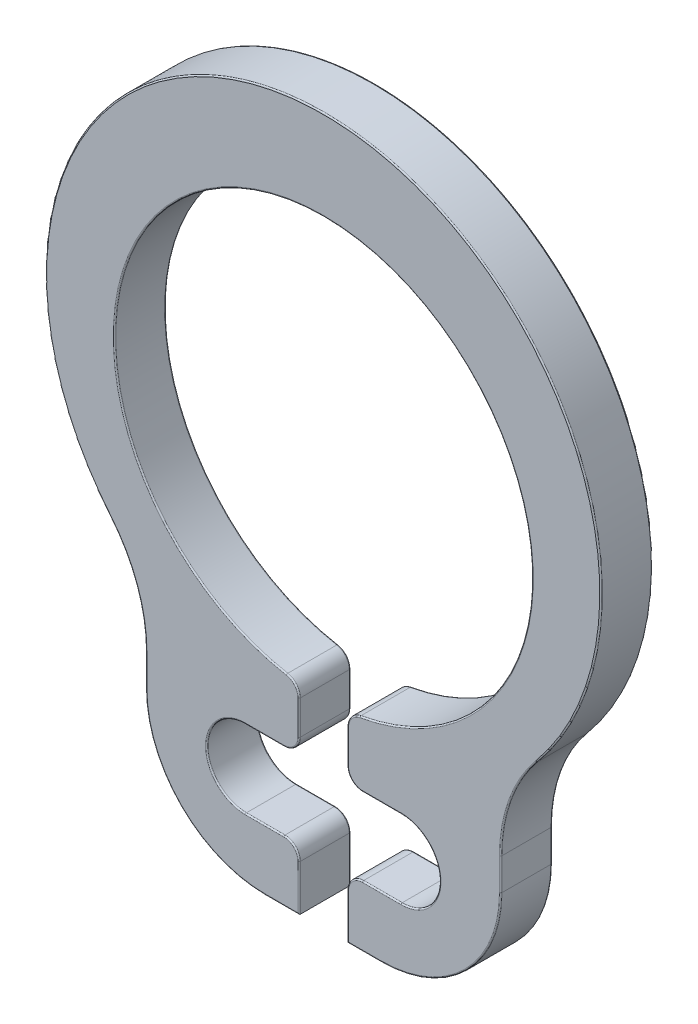
SolidWorks part; units mm, degrees
material "PLA"
ref_plane "Front Plane" through (0, 0, 0) normal (0, 0, 1) x (1, 0, 0)
ref_plane "Top Plane" through (0, 0, 0) normal (0, 1, 0) x (1, 0, 0)
ref_plane "Right Plane" through (0, 0, 0) normal (1, 0, 0) x (0, 0, -1)
sketch "Sketch1" plane through (0, 0, 0) normal (0, 0, 1) x (1, 0, 0)
  line L0 (0, 5.5) -> (0, -5.5) construction
  line L1 (-1.2125, -3.95) -> (1.2125, -3.95) construction
  line L2 (-1.2125, -3.35) -> (1.2125, -3.35)
  line L3 (-1.2125, -4.55) -> (1.2125, -4.55)
  line L4 (1.8125, -3.95) -> (2.7625, -3.95) construction
  line L5 (0, -2.4) -> (0, -3.35) construction
  circle A0 centre (0, 0.85) radius 3.25
  arc A3 (-1.2125, -3.35) -> (-1.2125, -4.55) centre (-1.2125, -3.95) ccw
  arc A4 (1.2125, -4.55) -> (1.2125, -3.35) centre (1.2125, -3.95) ccw
  circle A5 centre (0, 1.175) radius 4.325 construction
  circle A6 centre (0, 0.85) radius 3.5 construction
  circle A7 centre (0, 0.85) radius 3.35 construction
  point P6 (0, 4.1)
  point P7 (0, -2.4)
  point P10 (0, -3.95)
  dimension "For OD" = 7
  dimension "ID" = 6.5
  dimension "Band Width" = 1.4
  dimension "Tap Height" = 3.1
  dimension "Tap ID" = 1.2
  dimension "D3" = 1.55
  dimension "Tap Width Ref" = 5.525
  dimension "D1" = 0.325
sketch "Sketch2" plane through (0, 0, 0) normal (1, 0, 0) x (0, 0, -1)
  line L0 (-0.4, 5.5) -> (0.4, 5.5) construction
  line L1 (0, 7.2) -> (0, -5.5) construction
  line L2 (0, 5.5) -> (0, -5.5) construction
  line L3 (-0.45, 7.2) -> (0.45, 7.2) construction
  line L4 (-0.45, -5.5) -> (0.45, -5.5) construction
  dimension "Thickness" = 0.8
  dimension "For Groove Width" = 0.9
sketch "Sketch3" plane through (0, 0, 0) normal (0, 0, 1) x (1, 0, 0)
  line L0 (-1.2125, -4.55) -> (1.2125, -4.55) construction
  line L1 (-1.2125, -3.35) -> (1.2125, -3.35) construction
  line L2 (-1.2125, -4.55) -> (1.2125, -4.55)
  line L3 (-1.2125, -3.35) -> (1.2125, -3.35)
  line L4 (2.7625, -3.1428) -> (2.7625, -3.64)
  line L5 (-0.9025, -5.5) -> (0.9025, -5.5)
  line L6 (-2.7625, -3.1428) -> (-2.7625, -3.64)
  line L7 (-1.8125, -3.95) -> (-2.7625, -3.95) construction
  line L8 (1.8125, -3.95) -> (2.7625, -3.95) construction
  arc A0 (-1.2125, -3.35) -> (-1.2125, -4.55) centre (-1.2125, -3.95) ccw construction
  arc A1 (1.2125, -4.55) -> (1.2125, -3.35) centre (1.2125, -3.95) ccw construction
  arc A2 (-1.2125, -3.35) -> (-1.2125, -4.55) centre (-1.2125, -3.95) ccw
  arc A3 (1.2125, -4.55) -> (1.2125, -3.35) centre (1.2125, -3.95) ccw
  circle A4 centre (0, 0.85) radius 3.25 construction
  circle A5 centre (0, 0.85) radius 3.25
  arc A6 (-3.3234, -1.5928) -> (3.3234, -1.5928) centre (0, 1.175) cw
  arc A8 (3.3234, -1.5928) -> (2.7625, -3.1428) centre (5.1846, -3.1428) ccw
  arc A9 (2.7625, -3.64) -> (0.9025, -5.5) centre (0.9025, -3.64) cw
  arc A10 (-3.3234, -1.5928) -> (-2.7625, -3.1428) centre (-5.1846, -3.1428) cw
  arc A11 (-2.7625, -3.64) -> (-0.9025, -5.5) centre (-0.9025, -3.64) ccw
  circle A12 centre (0, 1.175) radius 4.325 construction
  dimension "D1" = 1.55
  dimension "D2" = 1.86
  dimension "D3" = 0.95
extrude "Boss-Extrude1" add sketch "Sketch3" along normal mid plane 0.8
sketch "Sketch4" plane through (0, 0, 0) normal (0, 0, 1) x (1, 0, 0)
  line L0 (0, 0.85) -> (0, -5.5)
extrude "Cut-Extrude-Thin1" cut sketch "Sketch4" against normal through all both and the other way through all thin thin type mid plane wall 0.75
fillet "Fillet2" radius 0.2375 6 edges at (0.375, -4.55, 0) (-0.375, -4.55, 0) (0.375, -3.35, 0) (0.375, -2.3783, 0) (-0.375, -3.35, 0) (-0.375, -2.3783, 0)
fillet "Fillet1" radius 0.02 52 edges at (-0.9125, -4.55, -0.4) (-1.8125, -3.95, -0.4) (-0.9125, -3.35, -0.4) (0, 4.1, -0.4) (0.9125, -3.35, -0.4) (1.8125, -3.95, -0.4) (0.9125, -4.55, -0.4) (0.375, -5.1438, -0.4) (0.6388, -5.5, -0.4) (2.2177, -4.9552, -0.4) (2.7625, -3.3914, -0.4) (2.907, -2.3186, -0.4) (0, 5.5, -0.4) (-2.907, -2.3186, -0.4) (-2.7625, -3.3914, -0.4) (-2.2177, -4.9552, -0.4) (-0.6388, -5.5, -0.4) (-0.375, -5.1438, -0.4) (-2.2177, -4.9552, 0.4) (-2.7625, -3.3914, 0.4) (-2.907, -2.3186, 0.4) (0, 5.5, 0.4) (2.907, -2.3186, 0.4) (2.7625, -3.3914, 0.4) (2.2177, -4.9552, 0.4) (0.6388, -5.5, 0.4) (0.375, -5.1438, 0.4) (0.9125, -4.55, 0.4) (1.8125, -3.95, 0.4) (0.9125, -3.35, 0.4) (0, 4.1, 0.4) (-0.9125, -3.35, 0.4) (-1.8125, -3.95, 0.4) (-0.9125, -4.55, 0.4) (-0.375, -5.1438, 0.4) (-0.6388, -5.5, 0.4) (-0.4446, -4.6196, -0.4) (-0.4446, -3.2804, -0.4) (-0.375, -2.8479, -0.4) (-0.4304, -2.4308, -0.4) (0.4304, -2.4308, -0.4) (0.375, -2.8479, -0.4) (0.4446, -3.2804, -0.4) (0.4446, -4.6196, -0.4) (0.4446, -3.2804, 0.4) (0.375, -2.8479, 0.4) (0.4304, -2.4308, 0.4) (-0.4304, -2.4308, 0.4) (-0.375, -2.8479, 0.4) (-0.4446, -3.2804, 0.4) (-0.4446, -4.6196, 0.4) (0.4446, -4.6196, 0.4)
equation "\"D3@Sketch1\"=\"Tap Height@Sketch1\"*0.5"
equation "\"D1@Sketch3\"=\"Tap Height@Sketch1\"*0.5"
equation "\"D2@Sketch3\"=\"Tap Height@Sketch1\"*0.6"
equation "\"D1@Boss-Extrude1\" = \"Thickness@Sketch2\""
equation "\"D1@Sketch1\"= \"ID@Sketch1\" * 0.05"
equation "\"D1@Fillet2\"=\"D3@Sketch3\"*0.25"
